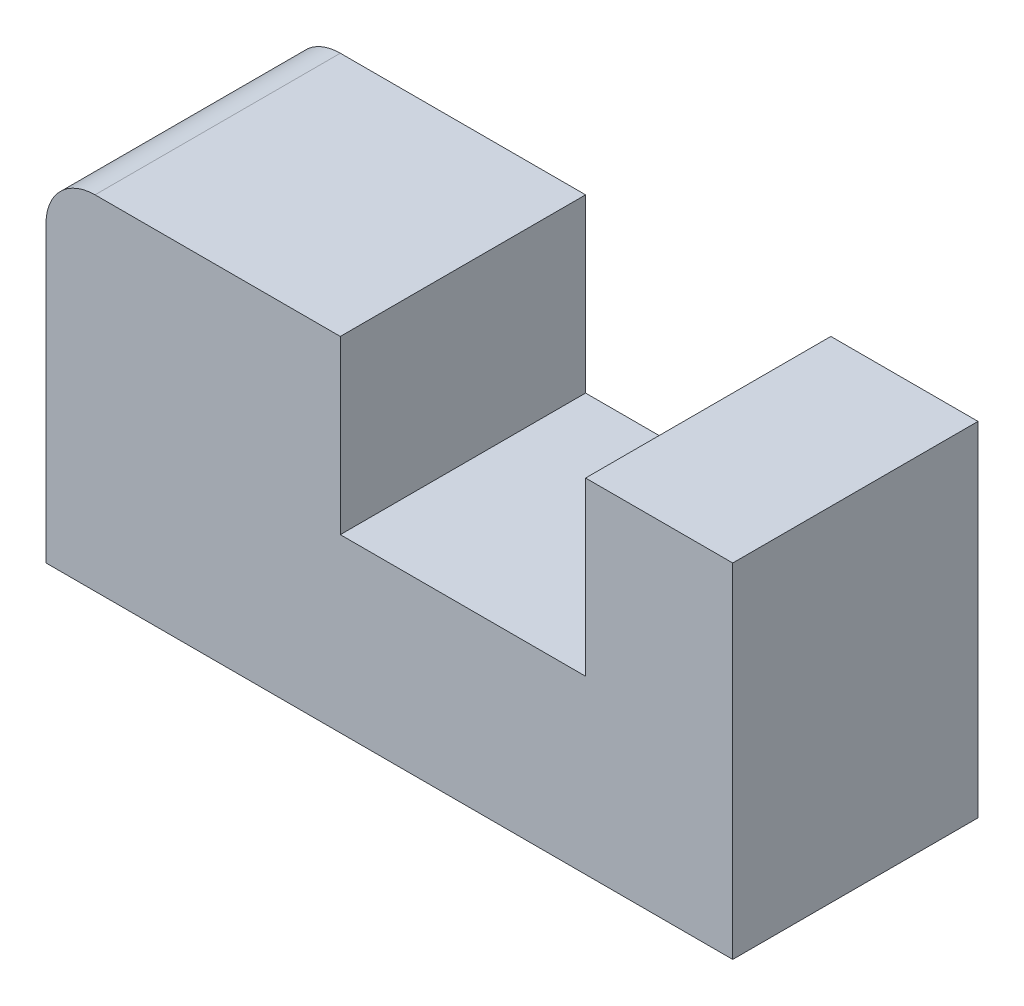
SolidWorks part; units mm, degrees
ref_plane "Plano frontal" through (0, 0, 0) normal (0, 0, 1) x (1, 0, 0)
ref_plane "Plano superior" through (0, 0, 0) normal (0, 1, 0) x (1, 0, 0)
ref_plane "Plano direito" through (0, 0, 0) normal (1, 0, 0) x (0, 0, -1)
sketch "Esboço1" plane through (0, 0, 0) normal (0, 0, 1) x (1, 0, 0)
  line L0 (-10, 35) -> (-70, 35)
  line L1 (70, -35) -> (-70, -35)
  line L2 (70, -35) -> (70, 35)
  line L3 (70, 35) -> (40, 35)
  line L4 (-70, -35) -> (-70, 35)
  line L5 (70, -35) -> (-70, 35) construction
  line L6 (70, 35) -> (-70, -35) construction
  line L8 (40, 35) -> (40, 0)
  line L9 (40, 0) -> (-10, 0)
  line L10 (-10, 35) -> (-10, 0)
  point P0 (0, 0)
  dimension "D1" = 140
  dimension "D2" = 70
  dimension "D3" = 30
  dimension "D4" = 50
  dimension "D5" = 35
extrude "Ressalto-extrusão1" add sketch "Esboço1" along normal blind 50
other "Limites1" [suppressed]
fillet "Filete1" radius 10 1 edges at (-70, 35, 25)
